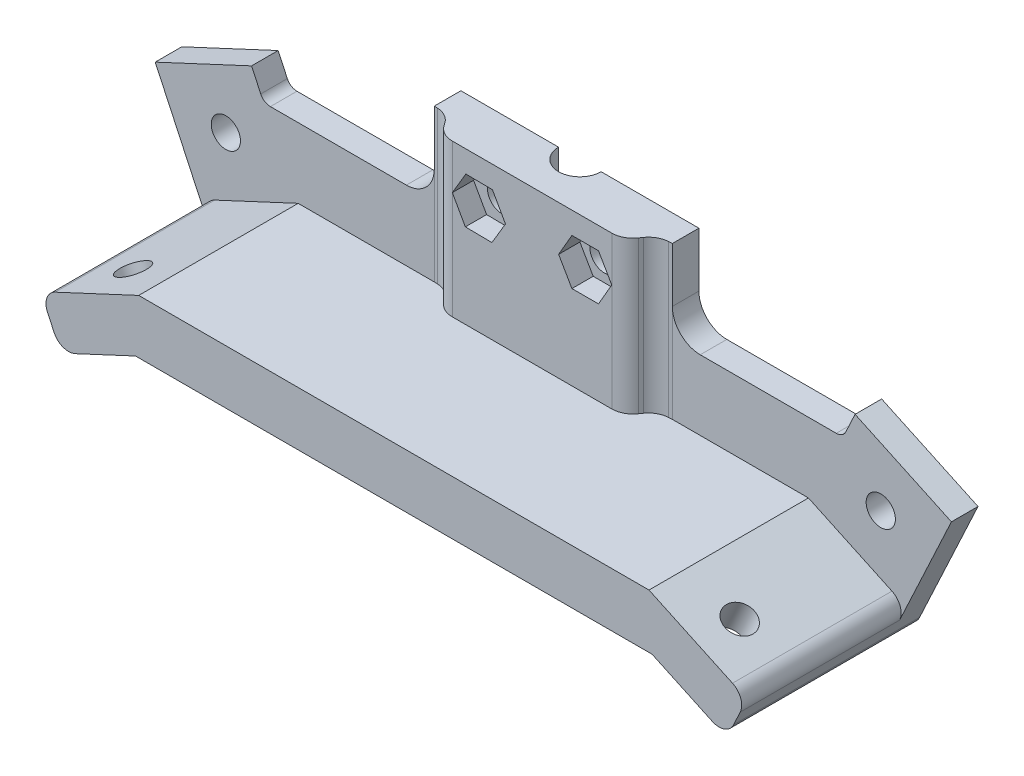
SolidWorks part; units mm, degrees
material "ABS"
ref_plane "Front Plane" through (0, 0, 0) normal (0, 0, 1) x (1, 0, 0)
ref_plane "Top Plane" through (0, 0, 0) normal (0, 1, 0) x (1, 0, 0)
ref_plane "Right Plane" through (0, 0, 0) normal (1, 0, 0) x (0, 0, -1)
sketch "Sketch1" plane through (0, 0, 0) normal (0, 0, 1) x (1, 0, 0)
  line L0 (0, 0) -> (44.78, 0)
  line L1 (44.78, 0) -> (44.78, -10.25)
  line L2 (50.03, -15.5) -> (75.6159, -15.5)
  line L3 (0, 0) -> (22.39, 0) construction
  line L4 (77.4285, -14.3452) -> (79.1575, -10.6372)
  line L5 (-26.2, -38.8219) -> (70.98, -38.8219)
  line L6 (79.1575, -10.6372) -> (97.2837, -19.0896)
  line L7 (97.2837, -19.0896) -> (86.2956, -42.6536)
  line L8 (-26.2, -38.8219) -> (-37.5288, -44.1047)
  line L9 (-41.5156, -42.6536) -> (-52.5037, -19.0896)
  line L10 (-52.5037, -19.0896) -> (-34.3775, -10.6372)
  line L11 (-34.3775, -10.6372) -> (-32.6485, -14.3452)
  line L12 (-30.8359, -15.5) -> (-5.25, -15.5)
  line L13 (0, -10.25) -> (0, 0)
  line L14 (-34.3775, -10.6372) -> (-24.8342, -43.5292) construction
  line L15 (82.3088, -44.1047) -> (70.98, -38.8219)
  line L16 (0, -8.45) -> (12.75, -8.45) construction
  line L17 (12.75, -8.45) -> (12.75, 0) construction
  line L18 (44.78, -8.45) -> (32.03, -8.45) construction
  line L19 (32.03, -8.45) -> (32.03, 0) construction
  line L20 (-43.4406, -14.8634) -> (-39.2144, -23.9265) construction
  line L21 (-39.2144, -23.9265) -> (-48.2775, -28.1527) construction
  line L22 (88.2206, -14.8634) -> (83.9944, -23.9265) construction
  line L23 (83.9944, -23.9265) -> (92.6151, -27.9464) construction
  arc A0 (-5.25, -15.5) -> (0, -10.25) centre (-5.25, -10.25) ccw
  arc A1 (44.78, -10.25) -> (50.03, -15.5) centre (50.03, -10.25) ccw
  arc A2 (-32.6485, -14.3452) -> (-30.8359, -15.5) centre (-30.8359, -13.5) ccw
  arc A3 (75.6159, -15.5) -> (77.4285, -14.3452) centre (75.6159, -13.5) ccw
  arc A4 (86.2956, -42.6536) -> (82.3088, -44.1047) centre (83.5767, -41.3857) cw
  arc A5 (-37.5288, -44.1047) -> (-41.5156, -42.6536) centre (-38.7967, -41.3857) cw
  circle A6 centre (12.75, -8.45) radius 2.75
  circle A7 centre (32.03, -8.45) radius 2.75
  circle A8 centre (-39.2144, -23.9265) radius 2.75
  circle A9 centre (83.9944, -23.9265) radius 2.75
  point P19 (0, -15.5)
  point P22 (44.78, -15.5)
  point P25 (-32.11, -15.5)
  point P28 (76.89, -15.5)
  point P31 (85.0278, -45.3725)
  point P34 (-40.2478, -45.3725)
  dimension "D15" = 5.25
  dimension "D16" = 5.25
  dimension "D17" = 2
  dimension "D18" = 3
  dimension "D21" = 5.5
  dimension "D23" = 5.5
  dimension "D25" = 5.5
  dimension "D27" = 5.5
  dimension "D1" = 44.78
  dimension "D2" = 97.18
  dimension "D3" = 54.5
  dimension "D4" = 20
  dimension "D5" = 15.5
  dimension "D6" = 15.5
  dimension "D7" = 109
  dimension "D8" = 115
  dimension "D9" = 20
  dimension "D10" = 29
  dimension "D11" = 29
  dimension "D12" = 115
  dimension "D13" = 15.5
  dimension "D14" = 15.5
  dimension "D19" = 12.75
  dimension "D20" = 8.45
  dimension "D22" = 12.75
  dimension "D24" = 10
  dimension "D26" = 10
extrude "Boss-Extrude1" add sketch "Sketch1" along normal blind 5 contours L12 A0 L13 L0 L1 A1 L2 A3 L4 L6 L7 A4 L15 L5 L8 A5 L9 L10 L11 A2
sketch "Sketch2" plane through (0, 0, 0) normal (0, 1, 0) x (1, 0, 0)
  line L0 (0, -5) -> (0.6541, -5.0343)
  line L1 (44.78, -5) -> (0, -5) construction
  line L2 (3.7214, -6.7345) -> (4.1134, -7.2943)
  line L3 (41.0586, -6.7345) -> (40.6666, -7.2943)
  line L5 (44.1259, -5.0343) -> (44.78, -5)
  line L6 (0, -5) -> (0, 0) construction
  line L10 (37.39, -9) -> (7.39, -9)
  line L11 (44.78, -5) -> (44.78, 0) construction
  line L12 (44.78, 0) -> (0, 0)
  line L13 (0, 0) -> (0, -5)
  line L14 (0, -5) -> (44.78, -5)
  line L15 (44.78, -5) -> (44.78, 0)
  line L18 (0, -5) -> (44.78, -5)
  arc A0 (41.0586, -6.7345) -> (44.1259, -5.0343) centre (44.3352, -9.0288) cw
  arc A1 (40.6666, -7.2943) -> (37.39, -9) centre (37.39, -5) cw
  arc A2 (4.1134, -7.2943) -> (7.39, -9) centre (7.39, -5) ccw
  arc A3 (0.6541, -5.0343) -> (3.7214, -6.7345) centre (0.4448, -9.0288) cw
  point P19 (39.4723, -9)
  point P22 (5.3077, -9)
  dimension "D2" = 4
  dimension "D1" = 30
  dimension "D3" = 52
  dimension "D4" = 35
  dimension "D5" = 4
  dimension "D6" = 93
  dimension "D7" = 93
  dimension "D8" = 0
extrude "Boss-Extrude2" add sketch "Sketch2" against normal blind 28.65 contours L10 A2 L2 A3 L0 L18 L5 A0 L3 A1
sketch "Sketch4" plane through (0, 0, 5) normal (0, 0, 1) x (1, 0, 0)
  line L0 (-25.61, -28.65) -> (22.39, -28.65)
  line L1 (-25.61, -28.65) -> (-41.3195, -35.9755)
  line L2 (-52.5037, -19.0896) -> (-41.5156, -42.6536) construction
  line L3 (70.39, -28.65) -> (86.0995, -35.9755)
  line L5 (-42.7706, -39.9623) -> (-41.5156, -42.6536)
  line L6 (-26.2, -38.8219) -> (70.98, -38.8219)
  line L7 (86.2956, -42.6536) -> (97.2837, -19.0896) construction
  line L9 (-26.2, -38.8219) -> (-37.5288, -44.1047)
  line L10 (87.5506, -39.9623) -> (86.2956, -42.6536)
  line L11 (70.98, -38.8219) -> (82.3088, -44.1047)
  line L12 (44.78, -28.65) -> (44.78, -10.25) construction
  line L13 (0, -28.65) -> (44.78, -28.65) construction
  line L14 (22.39, -28.65) -> (70.39, -28.65)
  arc A0 (86.0995, -35.9755) -> (87.5506, -39.9623) centre (84.8317, -38.6944) cw
  arc A1 (-41.3195, -35.9755) -> (-42.7706, -39.9623) centre (-40.0517, -38.6944) ccw
  arc A2 (82.3088, -44.1047) -> (86.2956, -42.6536) centre (83.5767, -41.3857) ccw
  arc A3 (-37.5288, -44.1047) -> (-41.5156, -42.6536) centre (-38.7967, -41.3857) cw
  point P19 (88.8185, -37.2433)
  point P33 (-44.0385, -37.2433)
  dimension "D1" = 3
  dimension "D4" = 3
  dimension "D5" = 3
  dimension "D6" = 3
  dimension "D2" = 48
  dimension "D3" = 48
extrude "Boss-Extrude3" add sketch "Sketch4" along normal blind 30 contours L6 L11 A2 L10 A0 L3 L14 L0 L1 A1 L5 A3 L9
sketch "Sketch5" plane through (0, 0, 0) normal (0, 1, 0) x (1, 0, 0)
  line L0 (44.78, 0) -> (0, 0) construction
  circle A0 centre (22.39, 0) radius 4
  dimension "D1" = 8
extrude "Cut-Extrude1" cut sketch "Sketch5" against normal blind 54.54
sketch "Sketch8" plane through (0, 0, 9) normal (0, 0, 1) x (1, 0, 0)
  line L0 (22.39, 0) -> (22.39, -28.65) construction
  line L1 (37.39, 0) -> (7.39, 0) construction
  line L2 (37.39, -28.65) -> (7.39, -28.65) construction
  line L3 (7.39, -8.4557) -> (37.39, -8.4557) construction
  line L4 (7.39, -28.65) -> (7.39, 0) construction
  line L5 (37.39, -28.65) -> (37.39, 0) construction
  line L7 (9.841, -12.7575) -> (14.841, -12.814)
  line L8 (14.841, -12.814) -> (17.39, -8.5122)
  line L9 (17.39, -8.5122) -> (14.939, -4.1538)
  line L10 (14.939, -4.1538) -> (9.939, -4.0973)
  line L11 (9.939, -4.0973) -> (7.39, -8.3991)
  line L12 (7.39, -8.3991) -> (9.841, -12.7575)
  line L13 (37.39, -8.4557) -> (34.89, -4.1255)
  line L14 (34.89, -4.1255) -> (29.89, -4.1255)
  line L15 (29.89, -4.1255) -> (27.39, -8.4557)
  line L16 (27.39, -8.4557) -> (29.89, -12.7858)
  line L17 (29.89, -12.7858) -> (34.89, -12.7858)
  line L18 (34.89, -12.7858) -> (37.39, -8.4557)
  circle A0 centre (12.39, -8.4557) radius 4.3304 construction
  circle A1 centre (32.39, -8.4557) radius 4.3301 construction
  dimension "D4" = 8.6608
  dimension "D1" = 8.4557
  dimension "D2" = 5
  dimension "D3" = 5
extrude "Cut-Extrude2" cut sketch "Sketch8" against normal blind 4 contours L17 L18 L13 L14 L15 L16 | L10 L11 L12 L7 L8 L9
sketch "Sketch11" plane through (-2.1922, -4.7012, 0) normal (-0.4226, -0.9063, 0) x (0.9063, -0.4226, 0)
  line L0 (80.7366, 35) -> (93.2366, 35) construction
  line L1 (80.7366, 35) -> (80.7366, 0) construction
  circle A0 centre (86.7366, 27) radius 6
  dimension "D2" = 12
  dimension "D1" = 8
extrude "Cut-Extrude5" cut sketch "Sketch11" against normal blind 3.08 contours A0
sketch "Sketch12" plane through (10.1902, -21.8529, 0) normal (0.4226, -0.9063, 0) x (0.9063, 0.4226, 0)
  line L0 (-40.1521, 35) -> (-52.6521, 35) construction
  line L7 (-40.1521, 35) -> (-40.1521, 0) construction
  circle A0 centre (-46.1521, 27) radius 6
  dimension "D1" = 12
  dimension "D2" = 8
sketch "Sketch13" plane through (6.3995, -13.7237, 0) normal (-0.4226, 0.9063, 0) x (0.9063, 0.4226, 0)
  line L0 (-35.3186, -35) -> (-52.6521, -35) construction
  line L1 (-35.3186, -35) -> (-35.3186, -5) construction
  circle A0 centre (-45.3186, -27) radius 2.75
  dimension "D1" = 5.5
  dimension "D2" = 8
  dimension "D3" = 10
extrude "Cut-Extrude7" cut sketch "Sketch13" against normal blind 10 contours A0
sketch "Sketch14" plane through (1.5985, 3.428, 0) normal (0.4226, 0.9063, 0) x (0.9063, -0.4226, 0)
  line L0 (75.903, -35) -> (93.2366, -35) construction
  line L2 (75.903, -35) -> (75.903, -5) construction
  circle A0 centre (85.903, -27) radius 2.75
  dimension "D1" = 5.5
  dimension "D2" = 8
  dimension "D3" = 10
extrude "Cut-Extrude8" cut sketch "Sketch14" against normal blind 10
extrude "Cut-Extrude9" cut sketch "Sketch12" against normal blind 5 contours A0
